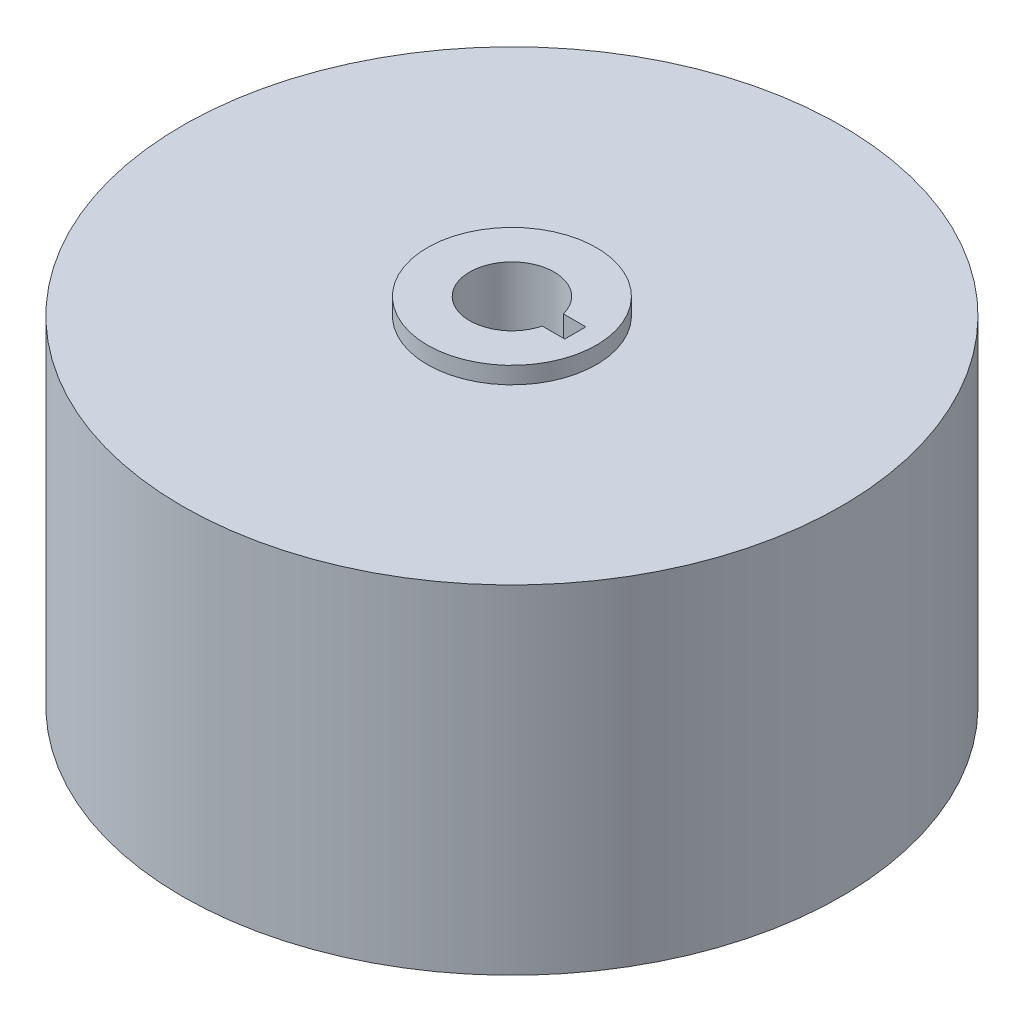
SolidWorks part; units mm, degrees
ref_plane "Front Plane" through (0, 0, 0) normal (0, 0, 1) x (1, 0, 0)
ref_plane "Top Plane" through (0, 0, 0) normal (0, 1, 0) x (1, 0, 0)
ref_plane "Right Plane" through (0, 0, 0) normal (1, 0, 0) x (0, 0, -1)
sketch "Sketch1" plane through (0, 0, 0) normal (0, 1, 0) x (1, 0, 0)
  circle A0 centre (0, 0) radius 39
  dimension "D1" = 78
extrude "Boss-Extrude1" add sketch "Sketch1" along normal blind 40
sketch "Sketch2" plane through (0, 40, 0) normal (0, 1, 0) x (1, 0, 0)
  circle A0 centre (0, 0) radius 10
  dimension "D1" = 20
extrude "Boss-Extrude2" add sketch "Sketch2" along normal blind 2 and the other way blind 42
sketch "Sketch3" plane through (0, 42, 0) normal (0, 1, 0) x (1, 0, 0)
  circle A0 centre (0, 0) radius 5
  dimension "D1" = 10
extrude "Cut-Extrude1" cut sketch "Sketch3" against normal through all and the other way through all
sketch "Sketch4" plane through (0, 42, 0) normal (0, 1, 0) x (1, 0, 0)
  line L1 (2.5, 1.25) -> (7.5, 1.25)
  line L2 (2.5, 1.25) -> (2.5, -1.25)
  line L3 (2.5, -1.25) -> (7.5, -1.25)
  line L4 (7.5, 1.25) -> (7.5, -1.25)
  line L5 (2.5, 1.25) -> (7.5, -1.25) construction
  line L6 (2.5, -1.25) -> (7.5, 1.25) construction
  circle A0 centre (0, 0) radius 5 construction
  point P0 (5, 0)
  dimension "D1" = 5
  dimension "D2" = 2.5
extrude "Cut-Extrude2" cut sketch "Sketch4" against normal through all
